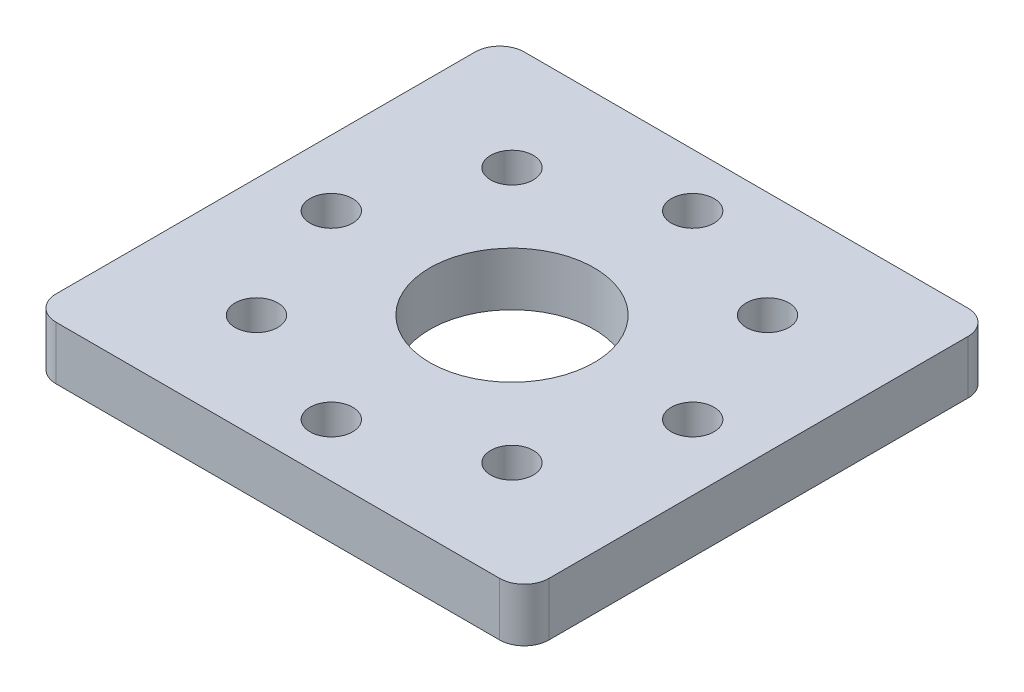
SolidWorks part; units mm, degrees
ref_plane "Front Plane" through (0, 0, 0) normal (0, 0, 1) x (1, 0, 0)
ref_plane "Top Plane" through (0, 0, 0) normal (0, 1, 0) x (1, 0, 0)
ref_plane "Right Plane" through (0, 0, 0) normal (1, 0, 0) x (0, 0, -1)
sketch "Sketch1" plane through (0, 0, 0) normal (0, 1, 0) x (1, 0, 0)
  line L1 (-15, 14.25) -> (15, 14.25)
  line L2 (-15, 14.25) -> (-15, -14.25)
  line L3 (-15, -14.25) -> (15, -14.25)
  line L4 (15, 14.25) -> (15, -14.25)
  dimension "D1" = 30
  dimension "D2" = 28.5
  dimension "D3" = 15
  dimension "D4" = 14.25
extrude "Boss-Extrude1" add sketch "Sketch1" against normal blind 3.15 and the other way blind 0.1
sketch "Sketch2" plane through (0, 0.1, 0) normal (0, 1, 0) x (1, 0, 0)
  circle A0 centre (0, 0) radius 5
  circle A1 centre (0, 11) radius 1.3
  circle A2 centre (7.7782, 7.7782) radius 1.3
  circle A3 centre (11, 0) radius 1.3
  circle A4 centre (7.7782, -7.7782) radius 1.3
  circle A5 centre (0, -11) radius 1.3
  circle A6 centre (-7.7782, -7.7782) radius 1.3
  circle A7 centre (-11, 0) radius 1.3
  circle A8 centre (-7.7782, 7.7782) radius 1.3
  point P22 (0, 0)
  dimension "D1" = 10
  dimension "D2" = 2.6
  dimension "D3" = 11
  dimension "D4" = 8
extrude "Cut-Extrude1" cut sketch "Sketch2" against normal through all
fillet "Fillet1" radius 1.5 4 edges at (15, -1.525, 14.25) (-15, -1.525, 14.25) (-15, -1.525, -14.25) (15, -1.525, -14.25)
equation "\"PLATE_WIDTH1\"= 30"
equation "\"D1@Sketch1\"=\"PLATE_WIDTH1\""
equation "\"PLATE_WIDTH2\"=28.5"
equation "\"D3@Sketch1\"=\"D1@Sketch1\"/2"
equation "\"D4@Sketch1\"=\"D2@Sketch1\"/2"
